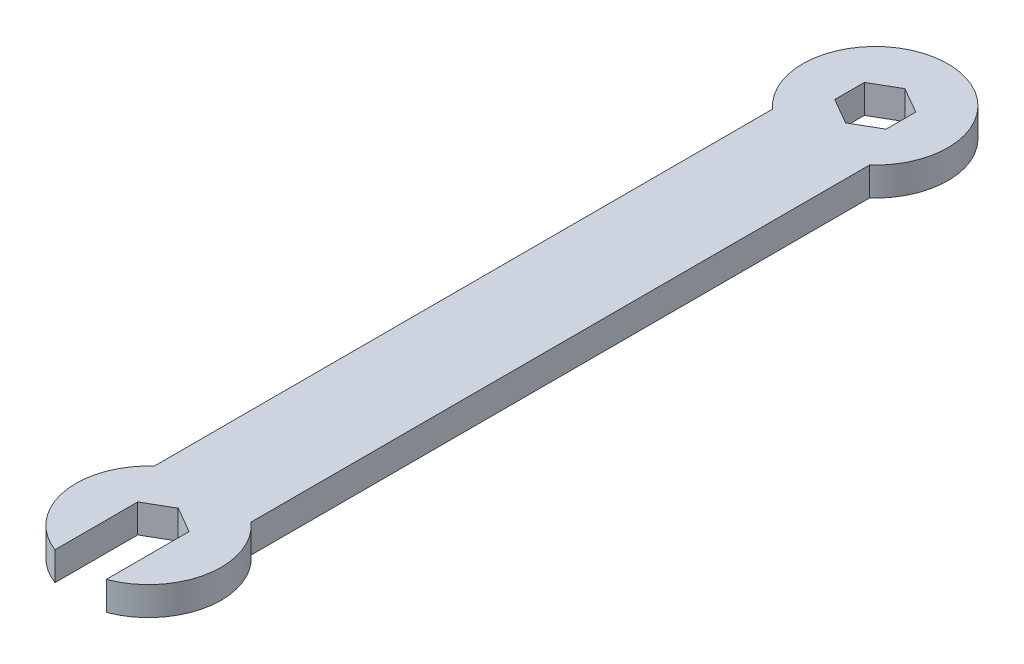
SolidWorks part; units mm, degrees
ref_plane "Front Plane" through (0, 0, 0) normal (0, 0, 1) x (1, 0, 0)
ref_plane "Top Plane" through (0, 0, 0) normal (0, 1, 0) x (1, 0, 0)
ref_plane "Right Plane" through (0, 0, 0) normal (1, 0, 0) x (0, 0, -1)
sketch "Sketch1" plane through (0, 0, 0) normal (0, 1, 0) x (1, 0, 0)
  line L1 (0, -3.06) -> (2.65, -1.53)
  line L2 (2.65, -1.53) -> (2.65, 1.53)
  line L3 (2.65, 1.53) -> (0, 3.06)
  line L4 (0, 3.06) -> (-2.65, 1.53)
  line L5 (-2.65, 1.53) -> (-2.65, -1.53)
  line L6 (-2.65, -1.53) -> (0, -3.06)
  line L7 (-5, 0) -> (5, 0)
  line L8 (-5, 0) -> (-5, -75)
  line L9 (-5, -75) -> (5, -75)
  line L10 (5, 0) -> (5, -75)
  line L11 (-5, 0) -> (5, -75) construction
  line L12 (-5, -75) -> (5, 0) construction
  line L13 (0, -78.06) -> (2.65, -76.53)
  line L14 (2.65, -82.0162) -> (2.65, -73.47)
  line L15 (2.65, -73.47) -> (0, -71.94)
  line L16 (0, -71.94) -> (-2.65, -73.47)
  line L17 (-2.65, -73.47) -> (-2.65, -82.0162)
  line L18 (-2.65, -76.53) -> (0, -78.06)
  circle A0 centre (0, 0) radius 2.65 construction
  circle A1 centre (0, 0) radius 7.5
  circle A2 centre (0, -75) radius 7.5
  circle A3 centre (0, -75) radius 2.65 construction
  point P14 (0, -37.5)
  dimension "D2" = 15
  dimension "D1" = 5.3
  dimension "D3" = 10
  dimension "D4" = 75
  dimension "D5" = 5.3
extrude "Boss-Extrude1" add sketch "Sketch1" along normal blind 2.95 contours L10 A2 L8 L9 L17 L16 L15 L14 | L8 A2 L17 L9 | L14 A2 L10 L9 | A2 L10 A1 L8 | L10 A1 L8 L7 L5 L4 L3 L2 | L8 A1 L10 L7 L2 L1 L6 L5
equation "\"wood\"= 2.95mm"
equation "\"slot_width\"= 10mm"
equation "\"slot_offset\"= 10mm"
equation "\"nut_width\"= 5.3mm"
equation "\"nut_height\"= 2.3mm"
equation "\"D1@Sketch1\"=\"nut_width\""
equation "\"D5@Sketch1\"=\"nut_width\""
equation "\"D1@Boss-Extrude1\"=\"wood\""
